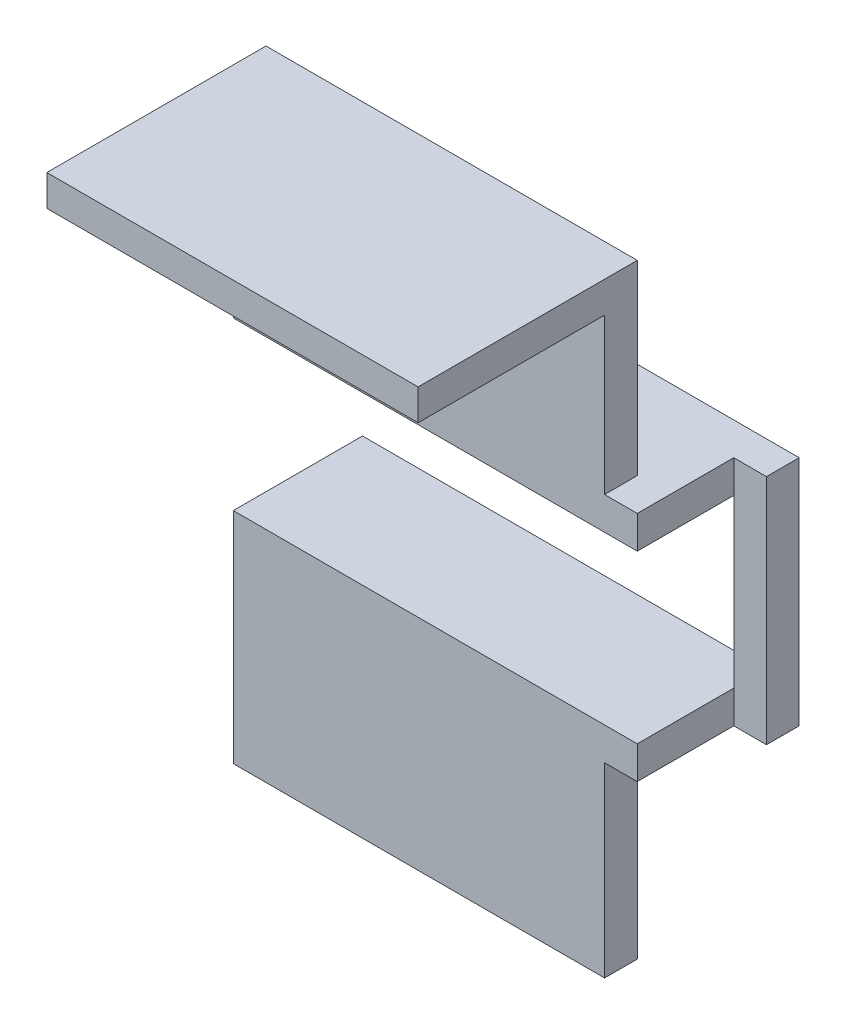
SolidWorks part; units mm, degrees
ref_plane "정면" through (0, 0, 0) normal (0, 0, 1) x (1, 0, 0)
ref_plane "윗면" through (0, 0, 0) normal (0, 1, 0) x (1, 0, 0)
ref_plane "우측면" through (0, 0, 0) normal (1, 0, 0) x (0, 0, -1)
sketch "스케치1" plane through (0, 0, 0) normal (0, 0, 1) x (1, 0, 0)
  line L1 (-5.9, 11.4) -> (5.9, 11.4)
  line L2 (-5.9, 11.4) -> (-5.9, -11.4)
  line L3 (-5.9, -11.4) -> (5.9, -11.4)
  line L4 (5.9, 11.4) -> (5.9, -11.4)
  line L5 (-5.9, 11.4) -> (5.9, -11.4) construction
  line L6 (-5.9, -11.4) -> (5.9, 11.4) construction
  point P4 (0, 0)
  point P5 (0, 0)
  dimension "D1" = 22.8
  dimension "D2" = 11.8
extrude "보스-돌출1" add sketch "스케치1" along normal blind 4
sketch "스케치2" plane through (0, 11.4, 0) normal (0, 1, 0) x (1, 0, 0)
  line L1 (-5.9, -4) -> (9.9, -4)
  line L2 (-5.9, -4) -> (-5.9, 0)
  line L3 (-5.9, 0) -> (9.9, 0)
  line L4 (9.9, -4) -> (9.9, 0)
  line L5 (-5.9, -4) -> (9.9, 0) construction
  line L6 (-5.9, 0) -> (9.9, -4) construction
  point P4 (2, -2)
  point P8 (0, 0)
  dimension "D1" = 4
  dimension "D2" = 15.8
extrude "보스-돌출2" add sketch "스케치2" along normal blind 2
sketch "스케치5" plane through (0, 13.4, 0) normal (0, 1, 0) x (1, 0, 0)
  line L1 (-5.9, 0) -> (9.9, 0)
  line L2 (-5.9, 0) -> (-5.9, -4)
  line L3 (-5.9, -4) -> (9.9, -4)
  line L4 (9.9, 0) -> (9.9, -4)
  line L5 (-5.9, 0) -> (9.9, -4) construction
  line L6 (-5.9, -4) -> (9.9, 0) construction
  point P4 (2, -2)
extrude "보스-돌출4" add sketch "스케치5" along normal blind 2
sketch "스케치6" plane through (0, 0, 0) normal (0, 0, -1) x (-1, 0, 0)
  line L1 (-9.9, 15.4) -> (5.9, 15.4)
  line L2 (-9.9, 15.4) -> (-9.9, 11.4)
  line L3 (-9.9, 11.4) -> (5.9, 11.4)
  line L4 (5.9, 15.4) -> (5.9, 11.4)
  line L5 (-9.9, 15.4) -> (5.9, 11.4) construction
  line L6 (-9.9, 11.4) -> (5.9, 15.4) construction
  point P4 (-2, 13.4)
  dimension "D1" = 4
  dimension "D2" = 15.8
extrude "보스-돌출5" add sketch "스케치6" along normal blind 11.8
sketch "스케치7" plane through (9.9, 0, 0) normal (1, 0, 0) x (0, 0, -1)
  line L1 (11.8, 11.4) -> (7.8, 11.4)
  line L2 (11.8, 11.4) -> (11.8, 25.6)
  line L3 (11.8, 25.6) -> (7.8, 25.6)
  line L4 (7.8, 11.4) -> (7.8, 25.6)
  line L5 (11.8, 11.4) -> (7.8, 25.6) construction
  line L6 (11.8, 25.6) -> (7.8, 11.4) construction
  point P4 (9.8, 18.5)
  dimension "D1" = 4
  dimension "D2" = 14.2
extrude "보스-돌출7" add sketch "스케치7" along normal blind 4
sketch "스케치8" plane through (-5.9, 0, 0) normal (-1, 0, 0) x (0, 0, 1)
  line L1 (0, 11.4) -> (4, 11.4)
  line L2 (0, 11.4) -> (0, -11.4)
  line L3 (0, -11.4) -> (4, -11.4)
  line L4 (4, 11.4) -> (4, -11.4)
  line L5 (0, 11.4) -> (4, -11.4) construction
  line L6 (0, -11.4) -> (4, 11.4) construction
  point P4 (2, 0)
extrude "보스-돌출8" add sketch "스케치8" along normal blind 33.6
mirror "대칭 복사3" about plane through (13.9, 25.6, -11.8) normal (0, -1, 0) of bodies 110
sketch "스케치10" plane through (-5.9, 0, 0) normal (-1, 0, 0) x (0, 0, 1)
  line L1 (-11.8, 15.4) -> (4, 15.4)
  line L2 (-11.8, 15.4) -> (-11.8, 11.4)
  line L3 (-11.8, 11.4) -> (4, 11.4)
  line L4 (4, 15.4) -> (4, 11.4)
  line L5 (-11.8, 15.4) -> (4, 11.4) construction
  line L6 (-11.8, 11.4) -> (4, 15.4) construction
  point P4 (-3.9, 13.4)
extrude "보스-돌출9" add sketch "스케치10" along normal blind 33.6
sketch "스케치11" plane through (-5.9, 0, 0) normal (-1, 0, 0) x (0, 0, 1)
  line L1 (-11.8, 39.8) -> (4, 39.8)
  line L2 (-11.8, 39.8) -> (-11.8, 35.8)
  line L3 (-11.8, 35.8) -> (4, 35.8)
  line L4 (4, 39.8) -> (4, 35.8)
  line L5 (-11.8, 39.8) -> (4, 35.8) construction
  line L6 (-11.8, 35.8) -> (4, 39.8) construction
  point P4 (-3.9, 37.8)
extrude "보스-돌출10" add sketch "스케치11" along normal blind 33.6
sketch "스케치12" plane through (0, 0, 4) normal (0, 0, 1) x (1, 0, 0)
  line L0 (5.9, 62.6) -> (5.9, 39.8) construction
  line L1 (-39.5, 62.6) -> (5.9, 62.6)
  line L2 (-39.5, 62.6) -> (-39.5, 58.8)
  line L3 (-39.5, 58.8) -> (5.9, 58.8)
  line L4 (5.9, 62.6) -> (5.9, 58.8)
  line L5 (-39.5, 62.6) -> (5.9, 58.8) construction
  line L6 (-39.5, 58.8) -> (5.9, 62.6) construction
  point P4 (-16.8, 60.7)
  dimension "D1" = 3.8
extrude "보스-돌출11" add sketch "스케치12" along normal blind 22.8
